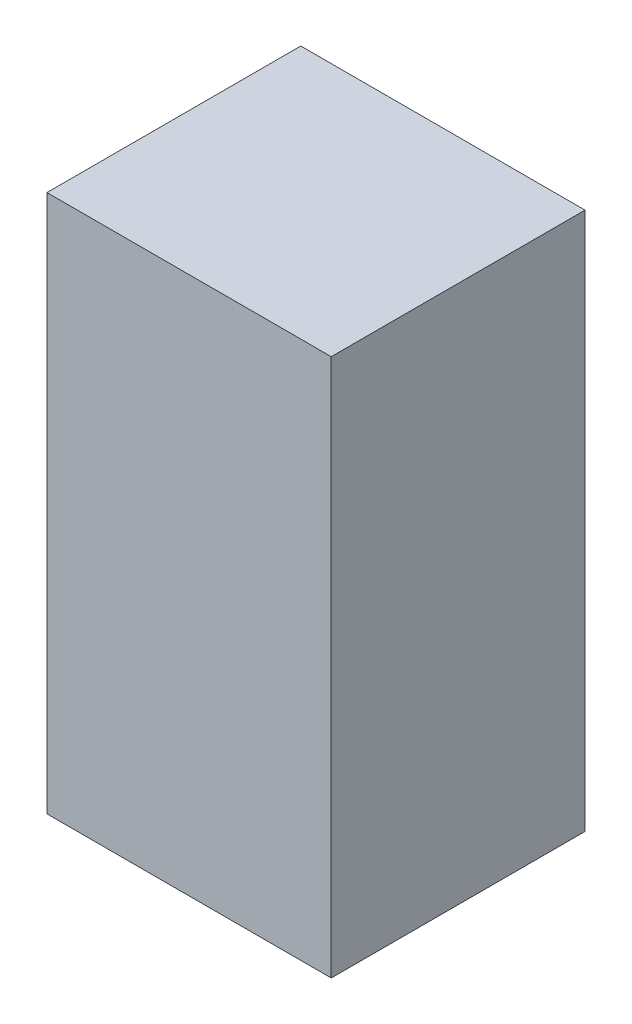
SolidWorks part; units mm, degrees
ref_plane "Front Plane" through (0, 0, 0) normal (0, 0, 1) x (1, 0, 0)
ref_plane "Top Plane" through (0, 0, 0) normal (0, 1, 0) x (1, 0, 0)
ref_plane "Right Plane" through (0, 0, 0) normal (1, 0, 0) x (0, 0, -1)
sketch "Sketch1" plane through (0, 0, 0) normal (0, 0, 1) x (1, 0, 0)
  line L1 (0, 0) -> (7.112, 0)
  line L2 (0, 0) -> (0, 13.462)
  line L3 (0, 13.462) -> (7.112, 13.462)
  line L4 (7.112, 0) -> (7.112, 13.462)
  dimension "D1" = 13.462
  dimension "D2" = 7.112
extrude "Boss-Extrude1" add sketch "Sketch1" along normal blind 6.35
